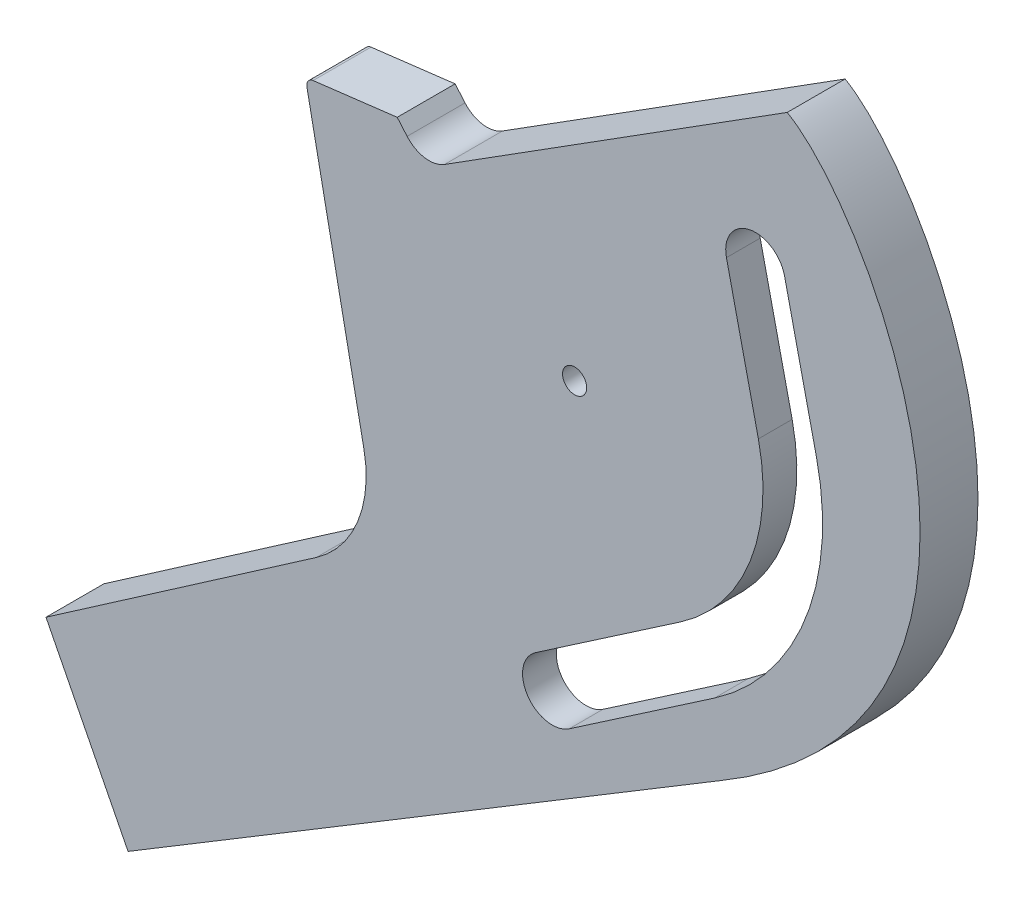
SolidWorks part; units mm, degrees
ref_plane "Front" through (0, 0, 0) normal (0, 0, 1) x (1, 0, 0)
ref_plane "Top" through (0, 0, 0) normal (0, 1, 0) x (1, 0, 0)
ref_plane "Right" through (0, 0, 0) normal (1, 0, 0) x (0, 0, -1)
sketch "Sketch1" plane through (0, 0, 0) normal (0, 0, 1) x (1, 0, 0)
  line L0 (-26.9556, 25.3594) -> (44.0508, 70.1983)
  line L1 (-34.7127, 26.5254) -> (-36.7655, 28.9177)
  line L2 (-36.7655, 28.9177) -> (-54.1949, 26.7961)
  line L3 (-55.4845, 25.0127) -> (-43.6679, -34.025)
  line L4 (-53.5518, -58.476) -> (-109.5463, -97.1922)
  line L5 (38.0775, 8.6273) -> (31.458, 37.8434)
  line L6 (-109.5463, -97.1922) -> (-92.5425, -130.7242)
  line L7 (-92.5425, -130.7242) -> (30.2552, -56.6109)
  line L8 (43.4964, 40.571) -> (50.116, 11.3549)
  line L9 (22.029, -32.2343) -> (-8.1037, -52.8271)
  line L10 (28.9936, -42.4254) -> (-1.1391, -63.0182)
  circle A0 centre (0, 0) radius 2.5
  arc A1 (22.029, -32.2343) -> (38.0775, 8.6273) centre (0, 0) ccw
  arc A2 (-31.6125, 22.9124) -> (-6.0284, 38.5744) centre (0, 0) ccw construction
  arc A3 (-45.8239, -23.2534) -> (12.0074, 49.9637) centre (0, 0) ccw construction
  arc A4 (43.4964, 40.571) -> (31.458, 37.8434) centre (37.4772, 39.2072) ccw
  arc A5 (-8.1037, -52.8271) -> (-1.1391, -63.0182) centre (-4.6214, -57.9226) ccw
  arc A6 (28.9936, -42.4254) -> (50.116, 11.3549) centre (0, 0) ccw
  arc A7 (-26.9556, 25.3594) -> (-34.7127, 26.5254) centre (-30.1592, 30.4326) cw
  arc A8 (-53.5518, -58.476) -> (-43.6679, -34.025) centre (-67.2012, -38.7353) ccw
  arc A9 (-55.4845, 25.0127) -> (-54.1949, 26.7961) centre (-54.0136, 25.3071) cw
  spline S0 degree 3 poles (44.0508, 70.1983) (62.0872, 60.1291) (102.2368, -14.3098) (30.2552, -56.6109) knots 0 0 0 0 1 1 1 1
  point P27 (-31.3377, 22.5922)
  point P30 (-40.5705, -49.5003)
  point P33 (-55.8023, 26.6004)
  dimension "D1" = 5
  dimension "D2" = 6
  dimension "D3" = 24
  dimension "D4" = 1.5
extrude "Boss-Extrude1" add sketch "Sketch1" against normal blind 12
sketch "Sketch3" plane through (0, 0, -12) normal (0, 0, -1) x (-1, 0, 0)
  line L0 (108.6334, -98.9925) -> (93.4495, -128.9356)
  line L14 (-29.2318, -54.8925) -> (91.7325, -127.8993)
  line L15 (91.7325, -127.8993) -> (106.9731, -97.8446)
  line L16 (106.9731, -97.8446) -> (52.4144, -60.121)
  line L17 (41.7068, -33.6325) -> (53.4174, 24.876)
  line L18 (53.4174, 24.876) -> (37.5863, 26.803)
  line L19 (37.5863, 26.803) -> (36.2305, 25.223)
  line L20 (25.8878, 23.6683) -> (-44.0657, 67.8424)
  line L21 (-29.2318, -54.8925) -> (91.7325, -127.8993)
  line L23 (106.9731, -97.8446) -> (52.4144, -60.121)
  line L24 (41.7068, -33.6325) -> (53.4174, 24.876)
  line L25 (53.4174, 24.876) -> (37.5863, 26.803)
  line L26 (37.5863, 26.803) -> (36.2305, 25.223)
  line L27 (25.8878, 23.6683) -> (-44.0657, 67.8424)
  line L28 (106.9731, -97.8446) -> (108.6334, -98.9925)
  line L29 (91.7325, -127.8993) -> (93.4495, -128.9356)
  arc A6 (41.7068, -33.6325) -> (52.4144, -60.121) centre (67.2012, -38.7353) ccw
  arc A7 (25.8878, 23.6683) -> (36.2305, 25.223) centre (30.1592, 30.4326) ccw
  arc A8 (41.7068, -33.6325) -> (52.4144, -60.121) centre (67.2012, -38.7353) ccw
  arc A9 (25.8878, 23.6683) -> (36.2305, 25.223) centre (30.1592, 30.4326) ccw
  spline S2 degree 3 poles (2240.8358, -1874.0546) (70.3051, 62.6302) (-16.6661, 90.9798) (-46.4871, 65.9605) (-47.0473, 65.4487) (-48.6768, 63.8665) (-49.6957, 62.7498) (-51.6431, 60.4338) (-52.5706, 59.2336) (-54.3517, 56.7652) (-55.2062, 55.4942) (-57.6422, 51.6374) (-59.1085, 48.9944) (-61.7722, 43.5859) (-62.9685, 40.8198) (-64.5622, 36.5793) (-65.0597, 35.1505) (-65.7539, 32.9835) (-65.9766, 32.2572) (-66.4043, 30.7965) (-66.6095, 30.061) (-67.5855, 26.3799) (-68.208, 23.4215) (-69.1242, 17.4766) (-69.4179, 14.4901) (-69.6479, 8.4866) (-69.5843, 5.4695) (-69.1862, 0.918) (-69.002, -0.6064) (-68.534, -3.6145) (-68.2499, -5.104) (-67.2468, -9.5287) (-66.377, -12.4201) (-64.7639, -16.6675) (-64.1747, -18.0684) (-63.2125, -20.1468) (-62.8781, -20.837) (-62.1877, -22.2002) (-61.8315, -22.8741) (-59.9965, -26.2052) (-58.3564, -28.7487) (-54.7619, -33.6141) (-52.8073, -35.9359) (-49.6574, -39.2648) (-48.5761, -40.3432) (-46.3668, -42.4313) (-45.237, -43.4429) (102.6878, -169.372) (622.4767, 187.2425) (-1367.1721, -2695.8067) knots -0.766573 -0.766573 -0.766573 -0.766573 0.015625 0.015625 0.03125 0.03125 0.0625 0.0625 0.09375 0.09375 0.125 0.125 0.1875 0.1875 0.25 0.25 0.28125 0.28125 0.296875 0.296875 0.3125 0.3125 0.375 0.375 0.4375 0.4375 0.5 0.5 0.53125 0.53125 0.5625 0.5625 0.625 0.625 0.65625 0.65625 0.671875 0.671875 0.6875 0.6875 0.75 0.75 0.8125 0.8125 0.84375 0.84375 0.875 0.875 4.852829 4.852829 4.852829 4.852829 only from (-44.0657, 67.8424) to (-29.2318, -54.8925)
  spline S3 degree 3 poles (-44.0657, 67.8424) (-44.712, 67.4094) (-45.3191, 66.9405) (-46.4871, 65.9605) (-47.0473, 65.4487) (-48.6768, 63.8665) (-49.6957, 62.7498) (-51.6431, 60.4338) (-52.5706, 59.2336) (-54.3517, 56.7652) (-55.2062, 55.4942) (-57.6422, 51.6374) (-59.1085, 48.9944) (-61.7722, 43.5859) (-62.9685, 40.8198) (-64.5622, 36.5793) (-65.0597, 35.1505) (-65.7539, 32.9835) (-65.9766, 32.2572) (-66.4043, 30.7965) (-66.6095, 30.061) (-67.5855, 26.3799) (-68.208, 23.4215) (-69.1242, 17.4766) (-69.4179, 14.4901) (-69.6479, 8.4866) (-69.5843, 5.4695) (-69.1862, 0.918) (-69.002, -0.6064) (-68.534, -3.6145) (-68.2499, -5.104) (-67.2468, -9.5287) (-66.377, -12.4201) (-64.7639, -16.6675) (-64.1747, -18.0684) (-63.2125, -20.1468) (-62.8781, -20.837) (-62.1877, -22.2002) (-61.8315, -22.8741) (-59.9965, -26.2052) (-58.3564, -28.7487) (-54.7619, -33.6141) (-52.8073, -35.9359) (-49.6574, -39.2648) (-48.5761, -40.3432) (-46.3668, -42.4313) (-45.237, -43.4429) (-39.4718, -48.3509) (-34.4912, -51.8017) (-29.2318, -54.8925) knots 0 0 0 0 0.015625 0.015625 0.03125 0.03125 0.0625 0.0625 0.09375 0.09375 0.125 0.125 0.1875 0.1875 0.25 0.25 0.28125 0.28125 0.296875 0.296875 0.3125 0.3125 0.375 0.375 0.4375 0.4375 0.5 0.5 0.53125 0.53125 0.5625 0.5625 0.625 0.625 0.65625 0.65625 0.671875 0.671875 0.6875 0.6875 0.75 0.75 0.8125 0.8125 0.84375 0.84375 0.875 0.875 1 1 1 1
  dimension "D1" = 2
extrude "Cut-Extrude2" cut sketch "Sketch3" against normal blind 5
sketch "Sketch2" plane through (0, 0, -7) normal (0, 0, -1) x (-1, 0, 0)
  circle A0 centre (0, 0) radius 20.407
  circle A4 centre (0, 0) radius 18.407
extrude "Cut-Extrude1" cut sketch "Sketch2" against normal blind 5
